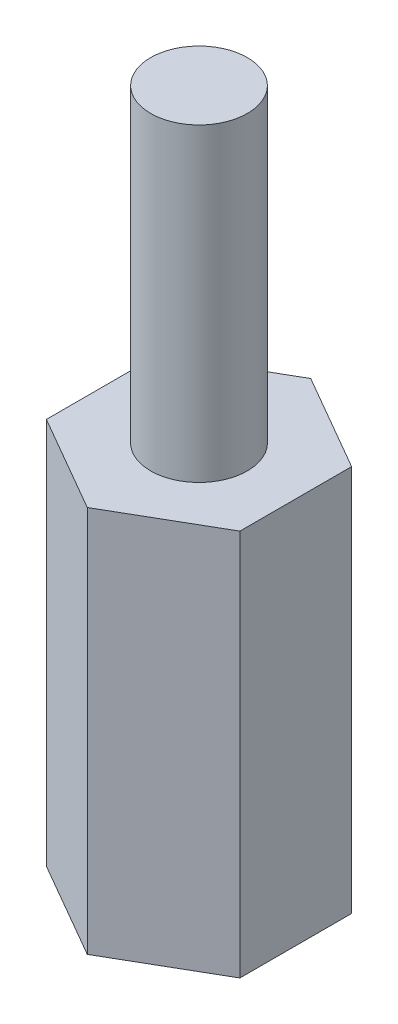
SolidWorks part; units mm, degrees
ref_plane "Front Plane" through (0, 0, 0) normal (0, 0, 1) x (1, 0, 0)
ref_plane "Top Plane" through (0, 0, 0) normal (0, 1, 0) x (1, 0, 0)
ref_plane "Right Plane" through (0, 0, 0) normal (1, 0, 0) x (0, 0, -1)
sketch "Sketch1" plane through (0, 0, 0) normal (0, 1, 0) x (1, 0, 0)
  line L1 (0, 2.8868) -> (-2.5, 1.4434)
  line L2 (-2.5, 1.4434) -> (-2.5, -1.4434)
  line L3 (-2.5, -1.4434) -> (0, -2.8868)
  line L4 (0, -2.8868) -> (2.5, -1.4434)
  line L5 (2.5, -1.4434) -> (2.5, 1.4434)
  line L6 (2.5, 1.4434) -> (0, 2.8868)
  circle A0 centre (0, 0) radius 2.5 construction
  dimension "D1" = 5
extrude "Boss-Extrude1" add sketch "Sketch1" along normal blind 10
sketch "Sketch2" plane through (0, 10, 0) normal (0, 1, 0) x (1, 0, 0)
  circle A0 centre (0, 0) radius 1.25
sketch "Sketch3" plane through (0, 0, 0) normal (0, -1, 0) x (-1, 0, 0)
  circle A0 centre (0, 0) radius 1.25
extrude "Boss-Extrude2" add sketch "Sketch2" along normal blind 8
extrude "Cut-Extrude1" cut sketch "Sketch3" against normal blind 8
